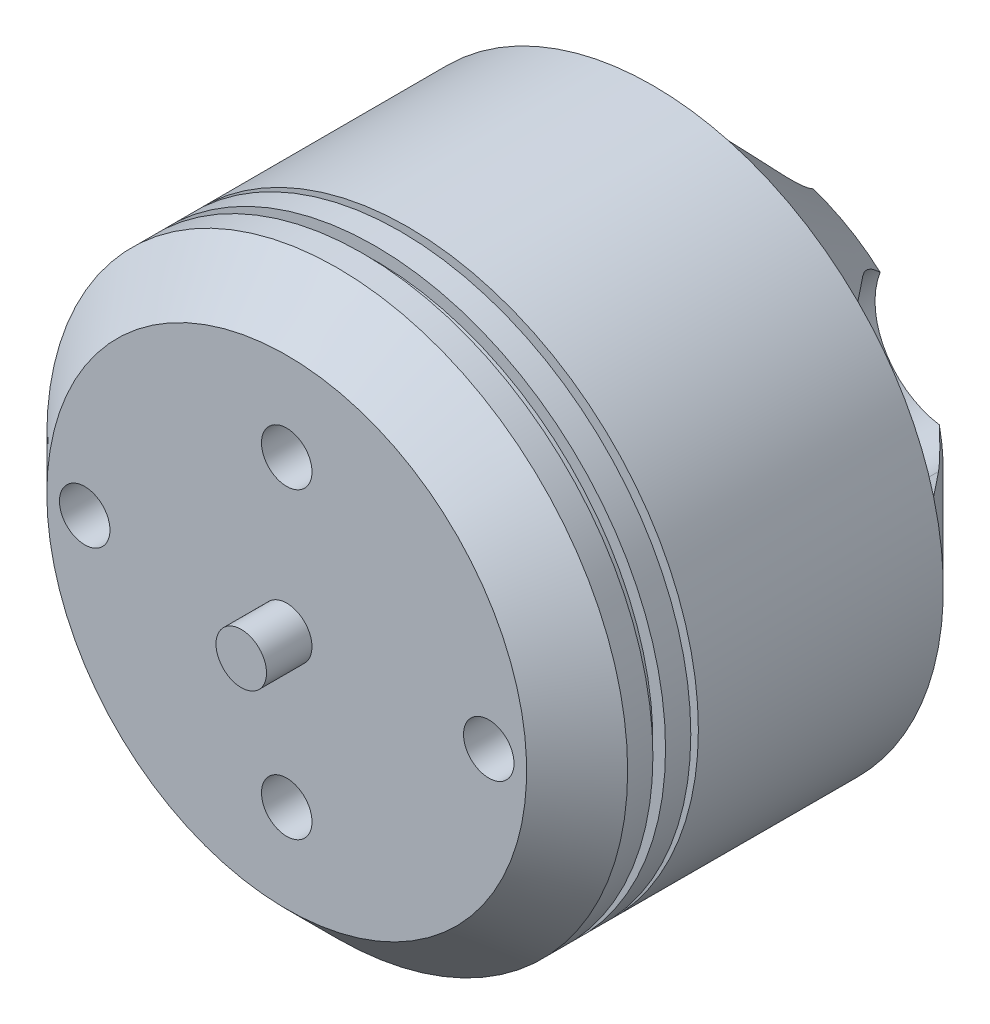
SolidWorks part; units mm, degrees
ref_plane "Front Plane" through (0, 0, 0) normal (0, 0, 1) x (1, 0, 0)
ref_plane "Top Plane" through (0, 0, 0) normal (0, 1, 0) x (1, 0, 0)
ref_plane "Right Plane" through (0, 0, 0) normal (1, 0, 0) x (0, 0, -1)
sketch "Sketch2" plane through (0, 0, 0) normal (0, 1, 0) x (1, 0, 0)
  line L0 (0, 20.7117) -> (0, 0)
  line L1 (1, -1.2883) -> (9.5, -1.2883)
  line L2 (9.5, -1.2883) -> (11.5, 0.7117)
  line L3 (11.5, 0.7117) -> (11.5, 1.7117)
  line L4 (11.5, 13.2117) -> (7.5, 17.2117)
  line L5 (7.5, 17.2117) -> (1, 17.2117)
  line L6 (1, 17.2117) -> (1, 20.7117)
  line L7 (1, 20.7117) -> (0, 20.7117)
  line L8 (0, 0) -> (0, -3.0883)
  line L9 (0, -3.0883) -> (1, -3.0883)
  line L10 (1, -3.0883) -> (1, -1.2883)
  line L11 (2.4547, 16.2117) -> (2.4547, 15.2117)
  line L12 (2.4547, 15.2117) -> (1.4547, 15.2117)
  line L13 (1.4547, 15.2117) -> (1.4547, 11.0928)
  line L14 (1.4547, 11.0928) -> (10.5, 11.0928)
  line L15 (10.5, 11.0928) -> (10.5, 12.7975)
  line L16 (10.5, 12.7975) -> (7.0858, 16.2117)
  line L17 (7.0858, 16.2117) -> (2.4547, 16.2117)
  line L18 (11.5, 1.7117) -> (11, 1.7117)
  line L19 (11, 1.7117) -> (11, 2.2117)
  line L20 (11, 2.2117) -> (11.5, 2.2117)
  line L21 (11.5, 3.2117) -> (9.5, 3.2117)
  line L22 (9.5, 3.2117) -> (9.5, 3.5117)
  line L23 (9.5, 3.5117) -> (11.5, 3.5117)
  line L24 (11.5, 3.5117) -> (11.5, 13.2117)
  line L25 (11.5, 2.2117) -> (11.5, 3.2117)
  dimension "D1" = 23.8
  dimension "D2" = 1.8
  dimension "D3" = 11.5
  dimension "D4" = 2
  dimension "D6" = 45
  dimension "D7" = 3.5
  dimension "D8" = 1
  dimension "D9" = 1
  dimension "D10" = 4
  dimension "D11" = 1
  dimension "D12" = 1
  dimension "D13" = 1
  dimension "D14" = 1
  dimension "D15" = 1
  dimension "D16" = 2
  dimension "D17" = 0.3
  dimension "D18" = 0.5
  dimension "D19" = 0.5
  dimension "D20" = 1
  dimension "D21" = 1
revolve "Revolve1" add sketch "Sketch2" angle 360 about L0
sketch "Sketch3" plane through (0, 0, -17.2117) normal (0, 0, -1) x (-1, 0, 0)
  line L0 (0, 0) -> (0, 9) construction
  line L1 (-3, 9) -> (-3, 16.652)
  line L2 (-3, 16.652) -> (3, 16.652)
  line L3 (3, 16.652) -> (3, 9)
  line L4 (15.921, 5.7279) -> (9.2942, 1.9019)
  line L5 (12.921, 10.9241) -> (15.921, 5.7279)
  line L6 (6.2942, 7.0981) -> (12.921, 10.9241)
  line L7 (12.921, -10.9241) -> (6.2942, -7.0981)
  line L8 (15.921, -5.7279) -> (12.921, -10.9241)
  line L9 (9.2942, -1.9019) -> (15.921, -5.7279)
  line L10 (-3, -16.652) -> (-3, -9)
  line L11 (3, -16.652) -> (-3, -16.652)
  line L12 (3, -9) -> (3, -16.652)
  line L13 (-15.921, -5.7279) -> (-9.2942, -1.9019)
  line L14 (-12.921, -10.9241) -> (-15.921, -5.7279)
  line L15 (-6.2942, -7.0981) -> (-12.921, -10.9241)
  line L16 (-12.921, 10.9241) -> (-6.2942, 7.0981)
  line L17 (-15.921, 5.7279) -> (-12.921, 10.9241)
  line L18 (-9.2942, 1.9019) -> (-15.921, 5.7279)
  circle A0 centre (0, 0) radius 4.5 construction
  circle A1 centre (0, 0) radius 12.8601 construction
  circle A2 centre (0, 4.5) radius 1
  circle A3 centre (4.5, 0) radius 1
  circle A4 centre (0, -4.5) radius 1
  circle A5 centre (-4.5, 0) radius 1
  arc A6 (-3, 9) -> (3, 9) centre (0, 9) ccw
  arc A7 (6.2942, 7.0981) -> (9.2942, 1.9019) centre (7.7942, 4.5) ccw
  arc A8 (9.2942, -1.9019) -> (6.2942, -7.0981) centre (7.7942, -4.5) ccw
  arc A9 (3, -9) -> (-3, -9) centre (0, -9) ccw
  arc A10 (-6.2942, -7.0981) -> (-9.2942, -1.9019) centre (-7.7942, -4.5) ccw
  arc A11 (-9.2942, 1.9019) -> (-6.2942, 7.0981) centre (-7.7942, 4.5) ccw
  dimension "D1" = 9
  dimension "D2" = 9
  dimension "D3" = 4
  dimension "D4" = 6
extrude "Cut-Extrude1" cut sketch "Sketch3" against normal blind 4
sketch "Sketch4" plane through (0, 0, 1.2883) normal (0, 0, 1) x (1, 0, 0)
  circle A0 centre (0, 0) radius 6 construction
  circle A1 centre (0, 0) radius 8 construction
  circle A2 centre (0, 6) radius 1
  circle A3 centre (0, -6) radius 1
  circle A4 centre (8, 0) radius 1
  circle A5 centre (-8, 0) radius 1
  dimension "D1" = 12
  dimension "D2" = 16
  dimension "D3" = 2
extrude "Cut-Extrude2" cut sketch "Sketch4" against normal blind 3
